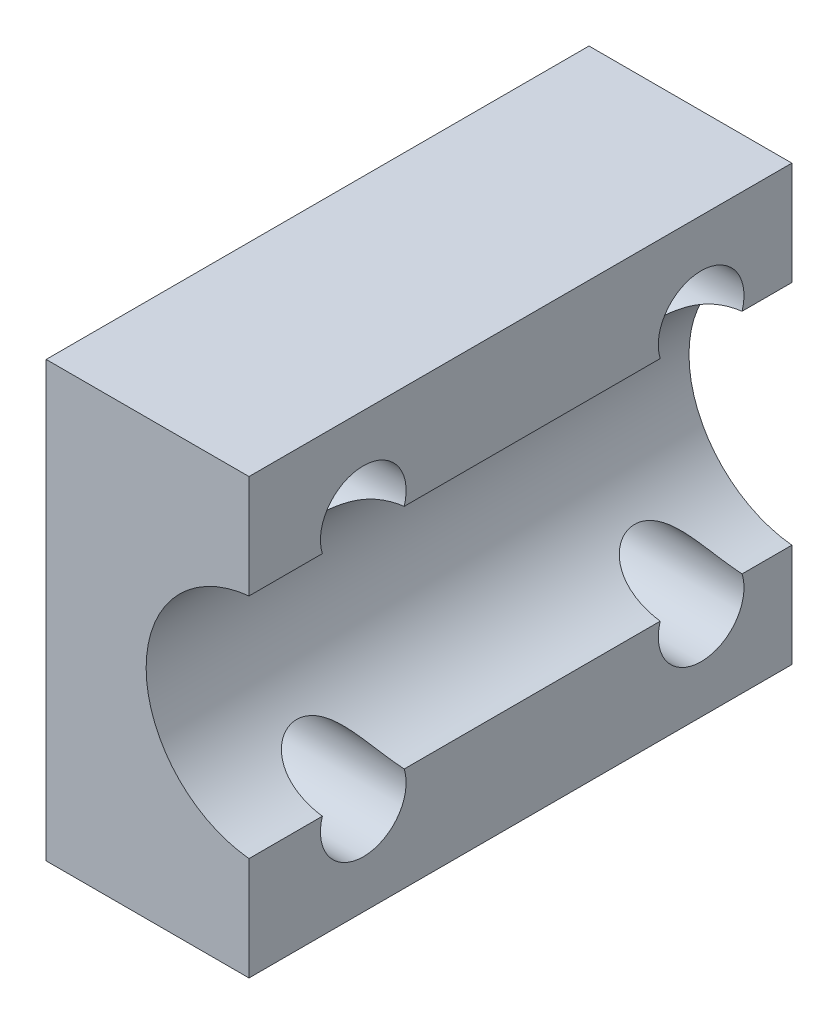
SolidWorks part; units mm, degrees
ref_plane "Front Plane" through (0, 0, 0) normal (0, 0, 1) x (1, 0, 0)
ref_plane "Top Plane" through (0, 0, 0) normal (0, 1, 0) x (1, 0, 0)
ref_plane "Right Plane" through (0, 0, 0) normal (1, 0, 0) x (0, 0, -1)
sketch "Sketch1" plane through (0, 0, 0) normal (0, 0, 1) x (1, 0, 0)
  line L0 (0, 4) -> (0, 7.6)
  line L1 (0, -4) -> (0, -7.6)
  line L2 (0, -7.6) -> (-7.5, -7.6)
  line L3 (0, 7.6) -> (-7.5, 7.6)
  line L4 (-7.5, 7.6) -> (-7.5, -7.6)
  circle A0 centre (0, 0) radius 4 construction
  arc A1 (0, 4) -> (0, -4) centre (0, 0) ccw
extrude "Extrude1" add sketch "Sketch1" along normal blind 19
sketch "Sketch2" plane through (-7.5, 0, 0) normal (1, 0, 0) x (0, 0, -1)
  line L0 (1.175, 4.425) -> (-22.6375, 4.425) construction
  line L1 (1.175, -4.425) -> (-22.6375, -4.425) construction
  line L2 (-15, 7.9375) -> (-15, -7.9375) construction
  line L3 (-3.175, 7.9375) -> (-3.175, -7.9375) construction
  line L4 (0, -7.6) -> (0, -4) construction
  line L5 (-19, -7.6) -> (-19, -4) construction
  line L6 (-19, -7.6) -> (0, -7.6) construction
  line L7 (-19, 7.6) -> (0, 7.6) construction
  circle A0 centre (-3.175, 4.425) radius 1.5
  circle A1 centre (-15, 4.425) radius 1.5
  circle A2 centre (-15, -4.425) radius 1.5
  circle A3 centre (-3.175, -4.425) radius 1.5
  dimension "D1" = 3.175
  dimension "D2" = 4
  dimension "D3" = 3.175
  dimension "D4" = 3.175
extrude "Extrude5" cut sketch "Sketch2" along normal through all
sketch "Sketch3" plane through (0, 0, 19) normal (0, 0, 1) x (1, 0, 0)
  line L0 (-0.4, 7.9375) -> (-0.4, -7.9375) construction
  line L1 (0, 4) -> (0, 7.6) construction
  line L2 (0, 7.6) -> (-0.4, 7.6)
  line L3 (0, 7.6) -> (-7.5, 7.6) construction
  line L4 (-0.4, 7.6) -> (-0.4, -7.6)
  line L5 (-7.5, -7.6) -> (0, -7.6) construction
  line L6 (-0.4, -7.6) -> (0, -7.6)
  line L7 (0, -7.6) -> (0, 7.6)
  dimension "D1" = 0.4
extrude "Extrude6" cut sketch "Sketch3" against normal through all
